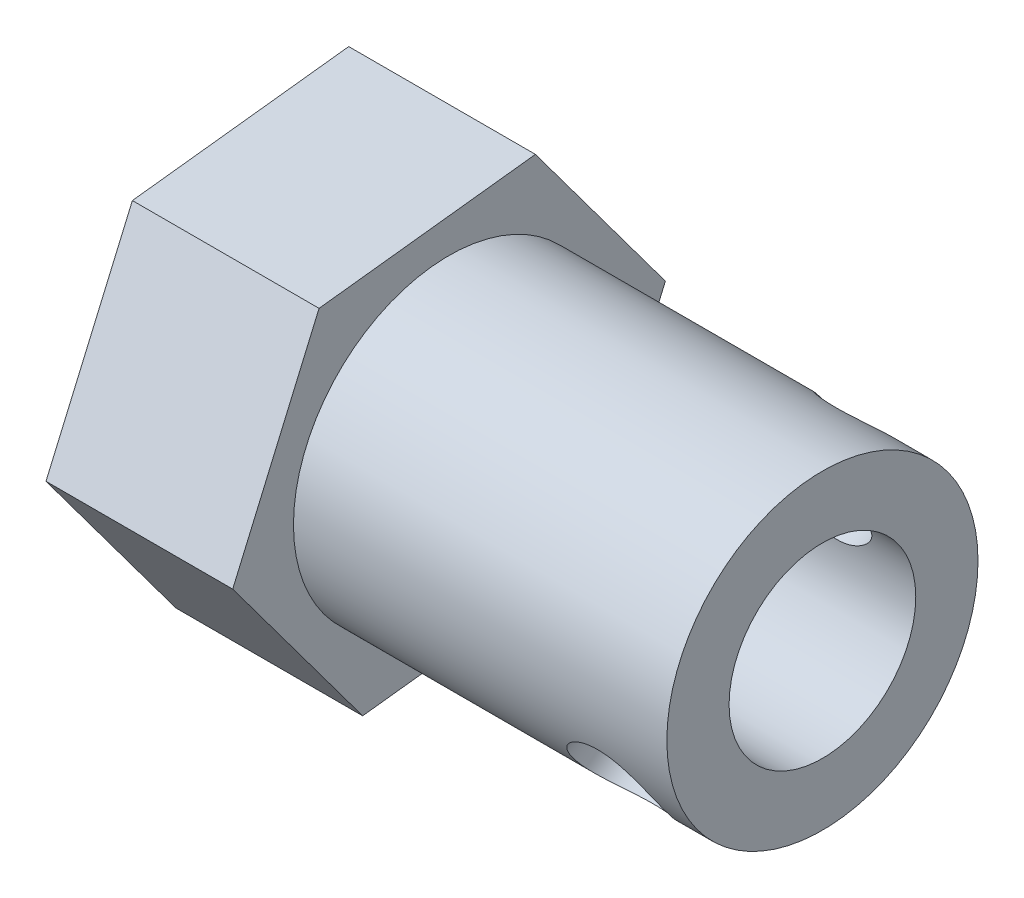
SolidWorks part; units mm, degrees
ref_plane "Front Plane" through (0, 0, 0) normal (0, 0, 1) x (1, 0, 0)
ref_plane "Top Plane" through (0, 0, 0) normal (0, 1, 0) x (1, 0, 0)
ref_plane "Right Plane" through (0, 0, 0) normal (1, 0, 0) x (0, 0, -1)
sketch "Sketch1" plane through (0, 0, 0) normal (1, 0, 0) x (0, 0, -1)
  circle A0 centre (0, 0) radius 5
  circle A1 centre (0, 0) radius 3
  dimension "D1" = 10
  dimension "D2" = 2
extrude "Boss-Extrude1" add sketch "Sketch1" along normal blind 18
sketch "Sketch2" plane through (0, 0, 0) normal (-1, 0, 0) x (0, 0, 1)
  line L1 (-6.9531, 0.8092) -> (-4.1774, -5.6169)
  line L2 (-4.1774, -5.6169) -> (2.7757, -6.4262)
  line L3 (2.7757, -6.4262) -> (6.9531, -0.8092)
  line L4 (6.9531, -0.8092) -> (4.1774, 5.6169)
  line L5 (4.1774, 5.6169) -> (-2.7757, 6.4262)
  line L6 (-2.7757, 6.4262) -> (-6.9531, 0.8092)
  circle A0 centre (0, 0) radius 6.0622 construction
  dimension "D1" = 7
extrude "Boss-Extrude2" add sketch "Sketch2" against normal blind 6
sketch "Sketch3" plane through (0, 0, 0) normal (-1, 0, 0) x (0, 0, 1)
  circle A0 centre (0, 0) radius 2
  dimension "D1" = 4
extrude "Cut-Extrude1" cut sketch "Sketch3" against normal blind 6
sketch "Sketch4" plane through (0, 3.6177, -4.8644) normal (0, 0.5968, -0.8024) x (-1, 0, 0)
  line L0 (8.8189, 0) -> (-23.2255, 0) construction
  line L1 (-18, 5) -> (-18, -5) construction
  circle A0 centre (-15.5, 0) radius 1.5
  point P3 (-15.5, 0)
  dimension "D2" = 3
  dimension "D1" = 2.5
extrude "Cut-Extrude2" cut sketch "Sketch4" against normal blind 14
